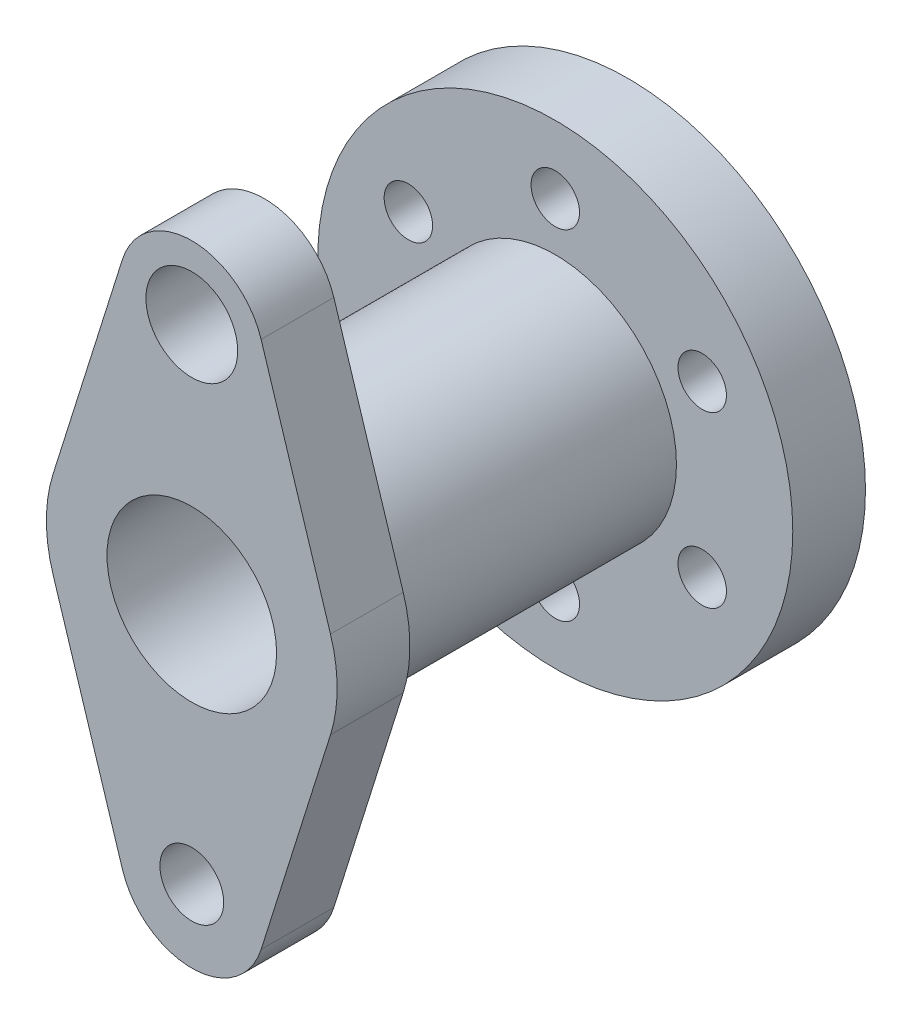
SolidWorks part; units mm, degrees
ref_plane "Front Plane" through (0, 0, 0) normal (0, 0, 1) x (1, 0, 0)
ref_plane "Top Plane" through (0, 0, 0) normal (0, 1, 0) x (1, 0, 0)
ref_plane "Right Plane" through (0, 0, 0) normal (1, 0, 0) x (0, 0, -1)
sketch "Sketch1" plane through (0, 0, 0) normal (0, 0, 1) x (1, 0, 0)
  line L0 (0, 54.8608) -> (0, -56.2431) construction
  circle A0 centre (0, 0) radius 35 construction
  circle A1 centre (0, 0) radius 49
  circle A3 centre (0, 35) radius 5
  circle A4 centre (-30.3109, 17.5) radius 5
  circle A5 centre (30.3109, 17.5) radius 5
  circle A6 centre (30.3109, -17.5) radius 5
  circle A7 centre (0, -35) radius 5
  circle A8 centre (-30.3109, -17.5) radius 5
  circle A9 centre (0, 0) radius 25
  dimension "D1" = 98
  dimension "D2" = 70
  dimension "D3" = 50
  dimension "D5" = 10
  dimension "D6" = 10
  dimension "D7" = 10
  dimension "D8" = 10
  dimension "D9" = 10
  dimension "D10" = 10
  dimension "D22" = 35
  dimension "D4" = 35
  dimension "D11" = 60.6218
  dimension "D12" = 30.3109
  dimension "D13" = 35
  dimension "D14" = 35
  dimension "D15" = 35
  dimension "D16" = 35
  dimension "D17" = 35
  dimension "D18" = 35
  dimension "D20" = 35
  dimension "D21" = 35
extrude "Boss-Extrude1" add sketch "Sketch1" along normal blind 15
sketch "Sketch2" plane through (0, 0, 0) normal (0, 0, 1) x (1, 0, 0)
  circle A1 centre (0, 0) radius 25
  circle A2 centre (0, 0) radius 13
  dimension "D1" = 26
  dimension "D2" = 50
extrude "Boss-Extrude2" add sketch "Sketch2" along normal blind 45
sketch "Sketch3" plane through (0, 0, 45) normal (0, 0, 1) x (1, 0, 0)
  circle A1 centre (0, 0) radius 17.5
  circle A2 centre (0, 0) radius 25
  dimension "D1" = 35
  dimension "D2" = 50
extrude "Boss-Extrude3" add sketch "Sketch3" along normal blind 30
ref_plane "Plane1" through (0, 0, 75) normal (0, 0, 1) x (1, 0, 0)
sketch "Sketch5" plane through (0, 0, 75) normal (0, 0, 1) x (1, 0, 0)
  line L0 (0, 50) -> (0, -50) construction
  line L1 (-89.0641, 0) -> (84.6519, 0) construction
  line L2 (28.7039, -8.7273) -> (14.3091, -54.5)
  line L3 (0, 74.7208) -> (0, -110.3466) construction
  line L4 (-28.7039, -8.7273) -> (-14.3091, -54.5)
  line L5 (28.7039, 8.7273) -> (14.3091, 54.5)
  line L6 (-28.7039, 8.7273) -> (-14.3091, 54.5)
  circle A0 centre (0, -50) radius 6.583
  circle A1 centre (0, 50) radius 9.4658
  arc A2 (-14.3091, -54.5) -> (14.3091, -54.5) centre (0, -50) ccw
  arc A3 (14.3091, 54.5) -> (-14.3091, 54.5) centre (0, 50) ccw
  circle A4 centre (0, 0) radius 30
  point P7 (-98.5744, -8.4816)
  dimension "D3" = 13.1659
  dimension "D4" = 18.9315
  dimension "D6" = 30
  dimension "D7" = 60
  dimension "D2" = 50
extrude "Boss-Extrude5" add sketch "Sketch5" along normal blind 15 contours A4 L4 A2 L2 A0 | A4 L5 A3 L6 A1 | A4
ref_plane "Plane2" through (0, 0, 90) normal (0, 0, 1) x (1, 0, 0)
sketch "Sketch6" plane through (0, 0, 90) normal (0, 0, 1) x (1, 0, 0)
  circle A0 centre (0, 0) radius 17.5
  dimension "D1" = 35
extrude "Cut-Extrude1" cut sketch "Sketch6" against normal blind 15
